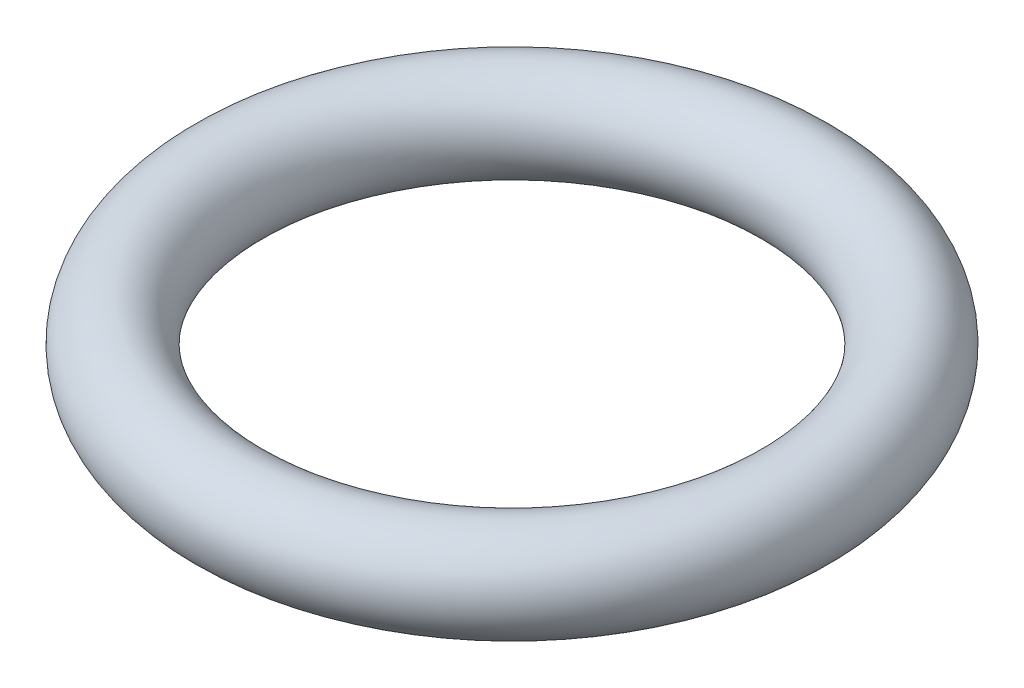
SolidWorks part; units mm, degrees
ref_plane "Front Plane" through (0, 0, 0) normal (0, 0, 1) x (1, 0, 0)
ref_plane "Top Plane" through (0, 0, 0) normal (0, 1, 0) x (1, 0, 0)
ref_plane "Right Plane" through (0, 0, 0) normal (1, 0, 0) x (0, 0, -1)
sketch "Sketch1" plane through (0, 0, 0) normal (0, 0, 1) x (1, 0, 0)
  line L0 (0, 0) -> (0, 69.4775) construction
  circle A0 centre (152.4, 0) radius 25.4
  dimension "D1" = 152.4
  dimension "D2" = 50.8
revolve "Revolve1" add sketch "Sketch1" angle 360 about L0
